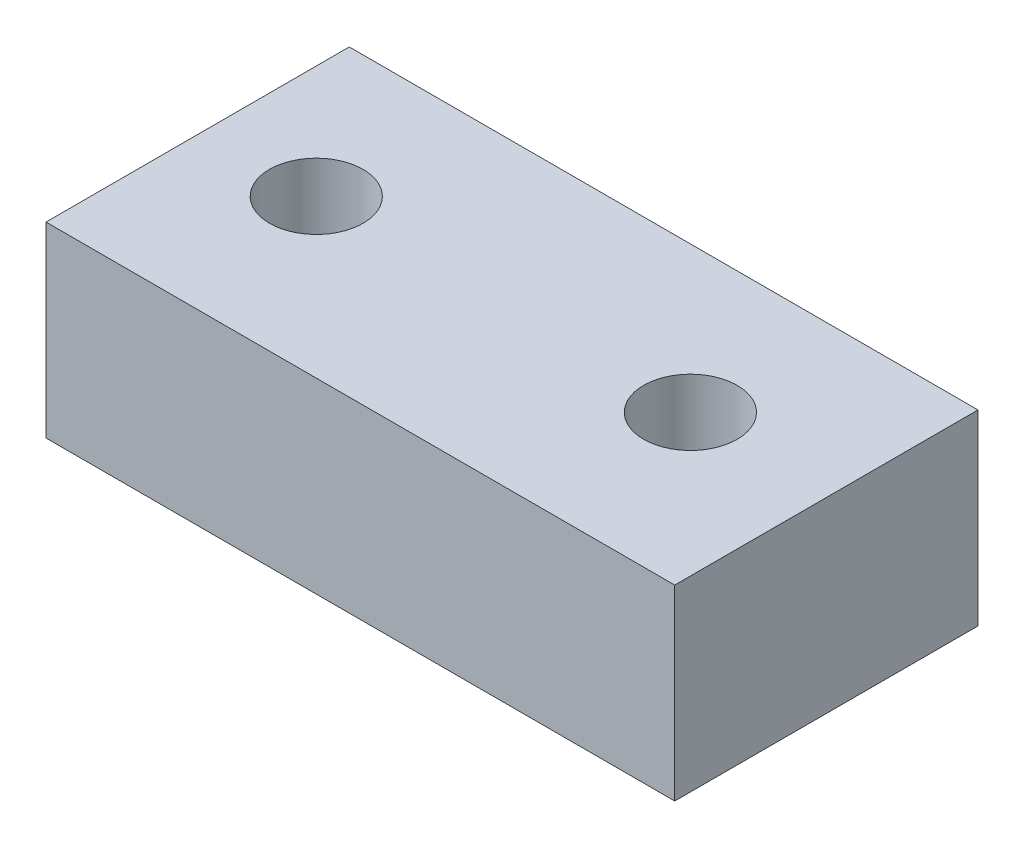
SolidWorks part; units mm, degrees
ref_plane "Front Plane" through (0, 0, 0) normal (0, 0, 1) x (1, 0, 0)
ref_plane "Top Plane" through (0, 0, 0) normal (0, 1, 0) x (1, 0, 0)
ref_plane "Right Plane" through (0, 0, 0) normal (1, 0, 0) x (0, 0, -1)
sketch "Sketch1" plane through (0, 0, 0) normal (0, 1, 0) x (1, 0, 0)
  line L0 (-4, 0) -> (4, 0)
  line L1 (-6.4131, 3.1189) -> (7.0304, 3.1189)
  line L2 (-6.4131, 3.1189) -> (-6.4131, -3.3659)
  line L3 (-6.4131, -3.3659) -> (7.0304, -3.3659)
  line L4 (7.0304, 3.1189) -> (7.0304, -3.3659)
  circle A0 centre (-4, 0) radius 1
  circle A1 centre (4, 0) radius 1
  point P8 (0, 0)
  point P11 (-6.4131, 3.1189)
  dimension "D1" = 2
  dimension "D2" = 8
extrude "Boss-Extrude1" add sketch "Sketch1" along normal blind 4
